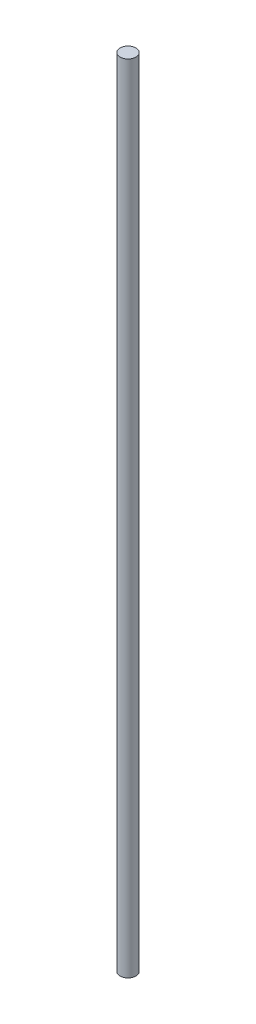
SolidWorks part; units mm, degrees
ref_plane "Front Plane" through (0, 0, 0) normal (0, 0, 1) x (1, 0, 0)
ref_plane "Top Plane" through (0, 0, 0) normal (0, 1, 0) x (1, 0, 0)
ref_plane "Right Plane" through (0, 0, 0) normal (1, 0, 0) x (0, 0, -1)
sketch "Sketch1" plane through (0, 0, 0) normal (0, 1, 0) x (1, 0, 0)
  line L0 (0, -4) -> (0, 4) construction
  line L1 (4, 0) -> (-4, 0) construction
  circle A0 centre (0, 0) radius 4
  dimension "D1" = 8
extrude "Boss-Extrude1" add sketch "Sketch1" along normal blind 400
